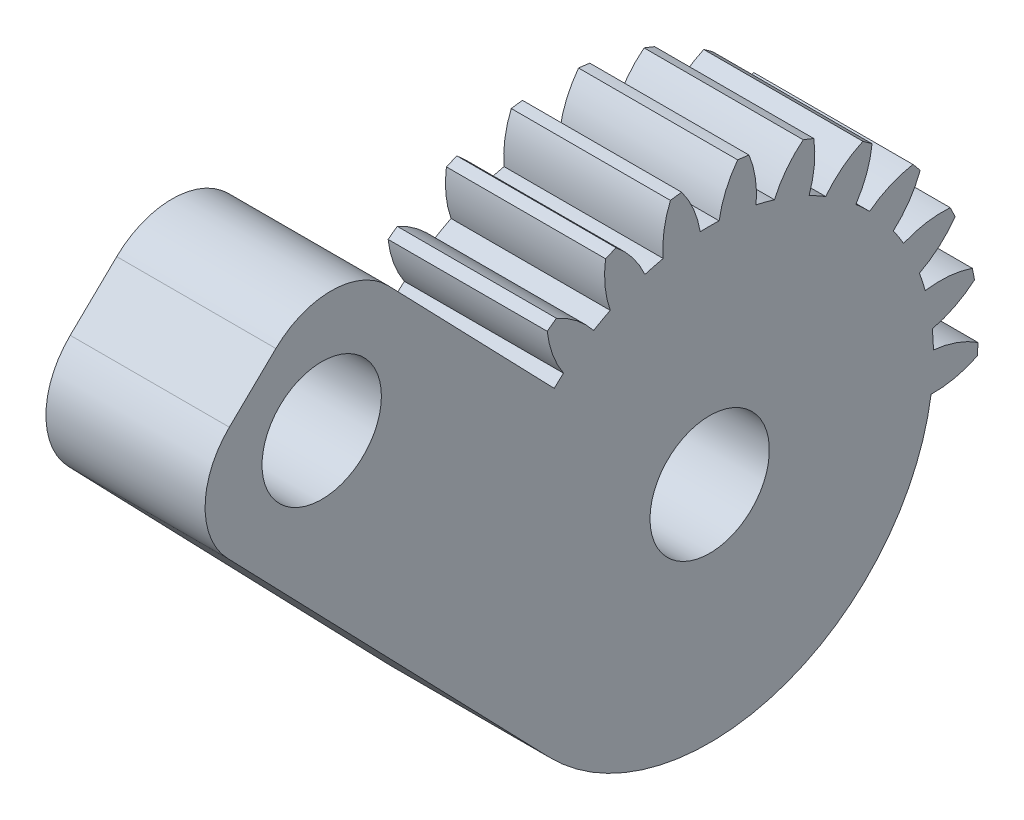
SolidWorks part; units mm, degrees
ref_plane "Plane1" through (0, 0, 0) normal (0, 0, 1) x (1, 0, 0)
ref_plane "Plane2" through (0, 0, 0) normal (0, 1, 0) x (1, 0, 0)
ref_plane "Plane3" through (0, 0, 0) normal (1, 0, 0) x (0, 0, -1)
other "Configuration Table"
sketch "HoldingSke" plane through (0, 0, 0) normal (0, 1, 0) x (1, 0, 0)
  line L0 (0, 0) -> (36.2523, -16.9047)
  line L1 (-15, 0) -> (100, 0) construction
  line L2 (0, 0) -> (-2.1039, 2.3779)
  line L3 (0, 0) -> (-11.863, 4.5341)
  line L4 (0, 0) -> (7.8269, 3.6497)
  line L5 (0, 0) -> (-46.8476, -17.4728)
  line L6 (0, 0) -> (-9.9476, -6.7116)
  line L7 (-2.1039, 2.3779) -> (8.6587, 51.2063)
  line L8 (-76.2, 54.61) -> (-73.9, 54.61)
  line L9 (-71.009, 38.7566) -> (-53.1078, 45.2721)
  line L10 (-76.2, 71.12) -> (104.1128, 71.12)
  line L11 (0, 0) -> (-12, 0)
  line L12 (-76.2, 101.6) -> (-76.113, 101.6)
  line L13 (24.9733, 27.94) -> (52.9518, 28.4284)
  line L14 (24.9733, 27.94) -> (24.9743, 27.94)
  line L15 (24.9733, 27.94) -> (100.4006, 29.5858)
  line L16 (-63.627, -2.5) -> (-12.827, -2.5)
  circle A0 centre (0, 0) radius 7.5
  circle A1 centre (0, 0) radius 28.124
  circle A2 centre (0, 0) radius 37.5
  circle A3 centre (0, 0) radius 7.5
  dimension "MHD" = 56.248
  dimension "Hub_dia" = 75
  dimension "Bore" = 15
  dimension "MBD" = 15
  dimension "Num_teeth" = 25
  dimension "Pitch" = 40
  dimension "Overall_len" = 50
  dimension "Show_teeth" = 25
  dimension "Thickness" = 12
  dimension "OAL" = 50.0005
  dimension "T_dim" = 2.3
  dimension "Ap" = 20
  dimension "H" = 19.05
  dimension "Pitch_radius" = 180.3128
  dimension "Width" = 12
  dimension "Backlash" = 0.087
  dimension "Addendum_fac" = 1
  dimension "Dedendum_fac" = 1.25
  dimension "Clearance_fac" = 0.25
  dimension "Dedendum_add" = 0.001
  dimension "Module" = 2.5
sketch "BasProSke" plane through (0, 0, 0) normal (0, 1, 0) x (1, 0, 0)
  line L0 (-10, 0) -> (60, 0) construction
  line L1 (0, 0) -> (0, 33.75)
  line L2 (0, 0) -> (20, 0)
  line L3 (20, 0) -> (20, 33.75)
  line L4 (20, 33.75) -> (0, 33.75)
  dimension "Thickness" = 20
  dimension "Diameter" = 67.5
revolve "Base-Revolve" add sketch "BasProSke" angle 134 about L0
sketch "TooCutSke" plane through (0, 0, 0) normal (1, 0, 0) x (0, 0, -1)
  line L1 (0, 0) -> (0, 107) construction
  line L2 (0, 0) -> (-2.1144, 31.1784) construction
  line L3 (0, 0) -> (-7.8202, 61.9031) construction
  line L4 (-2.1144, 31.1784) -> (-3.9101, 30.9515) construction
  arc A0 (1.1879, 28.0989) -> (-1.1879, 28.0989) centre (0, 0) ccw
  arc A1 (3.7021, 33.8019) -> (-3.7021, 33.8019) centre (0, 0) ccw
  circle A2 centre (0, 0) radius 31.25 construction
  circle A3 centre (0, 0) radius 29.3654 construction
  arc A4 (-1.1879, 28.0989) -> (-3.7021, 33.8019) centre (-13.5216, 26.0671) ccw
  arc A5 (3.7021, 33.8019) -> (1.1879, 28.0989) centre (13.5216, 26.0671) ccw
  dimension "Root_dia" = 56.248
  dimension "Overcut_dia" = 68.008
  dimension "Pitch_dia" = 62.5
  dimension "Base_dia" = 58.7308
  dimension "Flank_rad" = 12.5
  dimension "Half_ang" = 7.2
  dimension "Half_CT" = 1.81
extrude "ToothCut" cut sketch "TooCutSke" along normal through all
fillet "Breaks" [suppressed] radius 0.05
fillet "RootFillets" [suppressed] radius 0.626
pattern_circular "TeethCuts" count 25 every 14.4 about axis through (-10, 0, 0) along (1, 0, 0) of "ToothCut", "RootFillets", "Breaks"
sketch "HubNeaOneSke" plane through (0, 0, 0) normal (-1, 0, 0) x (0, 0, 1)
  circle A0 centre (0, 0) radius 28.124
  dimension "Diameter" = 56.248
extrude "HubNearOne" [suppressed] add sketch "HubNeaOneSke" along normal blind 30.0005
sketch "HubNeaBotSke" plane through (0, 0, 0) normal (-1, 0, 0) x (0, 0, 1)
  circle A0 centre (0, 0) radius 28.124
  dimension "Diameter" = 56.248
extrude "HubNearBoth" [suppressed] add sketch "HubNeaBotSke" along normal blind 15.0003
ref_plane "FarPln" through (20, 0, 0) normal (1, 0, 0) x (0, 0, -1)
sketch "HubFarSke" plane through (20, 0, 0) normal (1, 0, 0) x (0, 0, -1)
  circle A0 centre (0, 0) radius 28.124
  dimension "Diameter" = 56.248
extrude "HubFar" [suppressed] add sketch "HubFarSke" along normal blind 15.0003
sketch "BorSke" plane through (0, 0, 0) normal (1, 0, 0) x (0, 0, -1)
  circle A0 centre (0, 0) radius 7.5
  dimension "Diameter" = 15
extrude "Bore" cut sketch "BorSke" along normal mid plane 100.001
sketch "KeySke" plane through (0, 0, 0) normal (1, 0, 0) x (0, 0, -1)
  line L0 (-2.5, 0) -> (-2.5, 9.8)
  line L1 (-2.5, 9.8) -> (2.5, 9.8)
  line L2 (2.5, 9.8) -> (2.5, 0)
  line L3 (0, 0) -> (0, 34) construction
  line L4 (-2.5, 0) -> (2.5, 0)
  dimension "Offset" = 9.8
  dimension "Width" = 5
extrude "Keyway" [suppressed] cut sketch "KeySke" along normal mid plane 100.001
pattern_circular "Keyway2" [suppressed] count 2 every 90 about axis through (-10, 0, 0) along (1, 0, 0)
sketch "Sketch4" plane through (20, 0, 0) normal (1, 0, 0) x (0, 0, -1)
  line L0 (7.3622, -1.4311) -> (27.6073, -5.3663) construction
  line L1 (-19.5366, 20.2307) -> (-5.2099, 5.395)
  line L3 (7.3622, -1.4311) -> (27.6073, -5.3663)
  line L4 (-19.5366, 20.2307) -> (-47.3229, 49.0043)
  line L5 (-67.5536, 29.4677) -> (-20.2307, -19.5366)
  line L6 (-47.3229, 49.0043) -> (-67.5536, 29.4677)
  line L7 (7.3622, -1.4311) -> (27.6073, -5.3663) construction
  arc A0 (-19.5366, 20.2307) -> (27.6073, -5.3663) centre (0, 0) ccw
  arc A1 (-5.2099, 5.395) -> (7.3622, -1.4311) centre (0, 0) ccw
  dimension "D1" = 40
extrude "Boss-Extrude1" add sketch "Sketch4" against normal blind 20
sketch "Sketch5" plane through (20, 0, 0) normal (1, 0, 0) x (0, 0, -1)
  line L0 (-38.6397, 40.0126) -> (-58.8704, 20.476) construction
  line L4 (-47.3229, 49.0043) -> (-19.5366, 20.2307) construction
  line L5 (-67.5536, 29.4677) -> (-20.2307, -19.5366) construction
  line L7 (-47.3229, 49.0043) -> (-67.5536, 29.4677) construction
  circle A0 centre (-48.755, 30.2443) radius 7.5
  dimension "D1" = 15
  dimension "D2" = 12.5
extrude "Cut-Extrude1" cut sketch "Sketch5" against normal blind 20
fillet "Fillet1" radius 10 1 edges at (10, 49.0043, 47.3229)
fillet "Fillet2" radius 10 1 edges at (10, 29.4677, 67.5536)
scale "Scale1" scale about centroid uniform scaling yes scale factor 0.8
sketch "Sketch6" plane through (18, 0, 0) normal (1, 0, 0) x (0, 0, -1)
  circle A0 centre (-2.2873, 1.4035) radius 25 construction
  dimension "D1" = 50
equation "' \"Module@HoldingSke\" = 6.35"
equation "' \"Num_teeth@HoldingSke\" = 12"
equation "' \"Ap@HoldingSke\" =  20"
equation "' \"Ap@HoldingSke\" = 20"
equation "' \"Width@HoldingSke\" = 0.5 * 25.4"
equation "' \"Hub_dia@HoldingSke\"= 1 * 25.4"
equation "' \"Hub_dia@HoldingSke\" = 1 * 25.4"
equation "' \"Overall_len@HoldingSke\" = 1.0 * 25.4"
equation "' \"Bore@HoldingSke\" = 0.75 * 25.4"
equation "' \"T_dim@HoldingSke\" = 0.1 * 25.4"
equation "' \"Width@KeySke\" = 0.25 * 25.4"
equation "' \"Show_teeth@HoldingSke\" = 13"
equation "' \"Backlash@HoldingSke\" = 0.009 * 25.4"
equation "' \"Addendum_fac@HoldingSke\" = 1.0"
equation "' \"Dedendum_fac@HoldingSke\" = 1.25"
equation "' \"Dedendum_add@HoldingSke\" = 0.00005 * 25.4"
equation "' \"Clearance_fac@HoldingSke\" = 0.25"
equation "\"Pitch@HoldingSke\" = 1 / \"Module@HoldingSke\""
equation "\"Overcut_dia@TooCutSke\" = (\"Num_teeth@HoldingSke\" + 2 * \"Addendum_fac@HoldingSke\") / \"Pitch@HoldingSke\" + 0.002 * 25.4"
equation "\"Pitch_dia@TooCutSke\" = \"Num_teeth@HoldingSke\" / \"Pitch@HoldingSke\""
equation "\"Base_dia@TooCutSke\" = \"Num_teeth@HoldingSke\" / \"Pitch@HoldingSke\" * cos((\"Ap@HoldingSke\"  * 3.14159265 / 180))"
equation "\"Root_dia@TooCutSke\" = (\"Num_teeth@HoldingSke\" + 2) / \"Pitch@HoldingSke\" - 2 * (\"Addendum_fac@HoldingSke\" + \"Dedendum_fac@HoldingSke\") / \"Pitch@HoldingSke\" - \"Dedendum_add@HoldingSke\" * 2"
equation "\"Half_ang@TooCutSke\" = 180 / \"Num_teeth@HoldingSke\""
equation "\"Half_CT@TooCutSke\" = \"Num_teeth@HoldingSke\" / \"Pitch@HoldingSke\" * sin((3.14159265 / 2 / \"Num_teeth@HoldingSke\")) / 2 - 7 * \"Backlash@HoldingSke\" / 4"
equation "\"Flank_rad@TooCutSke\" = \"Num_teeth@HoldingSke\" / \"Pitch@HoldingSke\" / 5"
equation "\"Radius@RootFillets\" = \"Clearance_fac@HoldingSke\" / \"Pitch@HoldingSke\" + \"Dedendum_add@HoldingSke\""
equation "\"Break_rad@Breaks\" = 0.02 / \"Pitch@HoldingSke\""
equation "\"Thickness@HoldingSke\" = \"Width@HoldingSke\""
equation "\"OAL@HoldingSke\" = \"Thickness@HoldingSke\""
equation "\"MHD@HoldingSke\" = (\"Num_teeth@HoldingSke\" + 2) / \"Pitch@HoldingSke\" - 2 * (\"Addendum_fac@HoldingSke\" + \"Dedendum_fac@HoldingSke\")  / \"Pitch@HoldingSke\" - \"Dedendum_add@HoldingSke\" * 2"
equation "\"MBD@HoldingSke\" = (\"Num_teeth@HoldingSke\" + 2) / \"Pitch@HoldingSke\" - 2 * (\"Addendum_fac@HoldingSke\" + \"Dedendum_fac@HoldingSke\")  / \"Pitch@HoldingSke\" - \"Dedendum_add@HoldingSke\" * 2 - 0.002 * 25.4"
equation "\"MHD@HoldingSke\" = ((sgn( \"MHD@HoldingSke\" - \"Hub_dia@HoldingSke\" )-1)*( \"MHD@HoldingSke\" - \"Hub_dia@HoldingSke\" ))/-2+ \"Hub_dia@HoldingSke\""
equation "\"MBD@HoldingSke\" = ((sgn( \"MBD@HoldingSke\" - \"Bore@HoldingSke\" )-1)*( \"MBD@HoldingSke\" - \"Bore@HoldingSke\" ))/-2+ \"Bore@HoldingSke\""
equation "\"OAL@HoldingSke\" = ((sgn( \"OAL@HoldingSke\" - \"Overall_len@HoldingSke\" )+1)*( \"OAL@HoldingSke\" - \"Overall_len@HoldingSke\" ))/2 + \"Overall_len@HoldingSke\" + 0.000002 * 25.4"
equation "\"Num_teeth@TeethCuts\" = int( \"Show_teeth@HoldingSke\" ) + 1"
equation "\"Num_teeth@TeethCuts\" = ((sgn( \"Num_teeth@TeethCuts\" - \"Num_teeth@HoldingSke\" )-1)*( \"Num_teeth@TeethCuts\" - \"Num_teeth@HoldingSke\" ))/-2+ \"Num_teeth@HoldingSke\""
equation "\"Num_teeth@TeethCuts\" = ((sgn( \"Num_teeth@TeethCuts\" - 2.0)+1)*( \"Num_teeth@TeethCuts\" - 2.0))/2 +2.0"
equation "\"Angle@TeethCuts\" = 360.0 / \"Num_teeth@HoldingSke\""
equation "\"Diameter@BasProSke\" = (\"Num_teeth@HoldingSke\" + 2 * \"Addendum_fac@HoldingSke\") / \"Pitch@HoldingSke\""
equation "' \"Fillet_rad@BasProSke\" =  \"Thickness@HoldingSke\" * 0.05"
equation "' \"Fillet_rad@BasProSke\" = \"Thickness@HoldingSke\" * 0.05"
equation "\"MHD@HoldingSke\" = ((sgn( \"MHD@HoldingSke\" - \"Root_dia@TooCutSke\" )-1)*( \"MHD@HoldingSke\" - \"Root_dia@TooCutSke\" ))/-2+ \"Root_dia@TooCutSke\""
equation "\"Diameter@HubNeaOneSke\" = \"MHD@HoldingSke\""
equation "\"Length@HubNearOne\" = \"OAL@HoldingSke\" - \"Thickness@BasProSke\""
equation "\"Diameter@HubNeaBotSke\" = \"MHD@HoldingSke\""
equation "\"Length@HubNearBoth\" = ( \"OAL@HoldingSke\" - \"Thickness@BasProSke\" ) / 2.0"
equation "\"Thickness@FarPln\" = \"Thickness@BasProSke\""
equation "\"Diameter@HubFarSke\" = \"MHD@HoldingSke\""
equation "\"Length@HubFar\" = ( \"OAL@HoldingSke\" - \"Thickness@BasProSke\" ) / 2.0"
equation "\"Diameter@BorSke\" = \"MBD@HoldingSke\""
equation "\"D1@Bore\" = \"OAL@HoldingSke\" * 2.0"
equation "\"D1@Keyway\" = \"OAL@HoldingSke\" * 2.0"
equation "\"Offset@KeySke\" = \"T_dim@HoldingSke\" + \"MBD@HoldingSke\" / 2.0"
